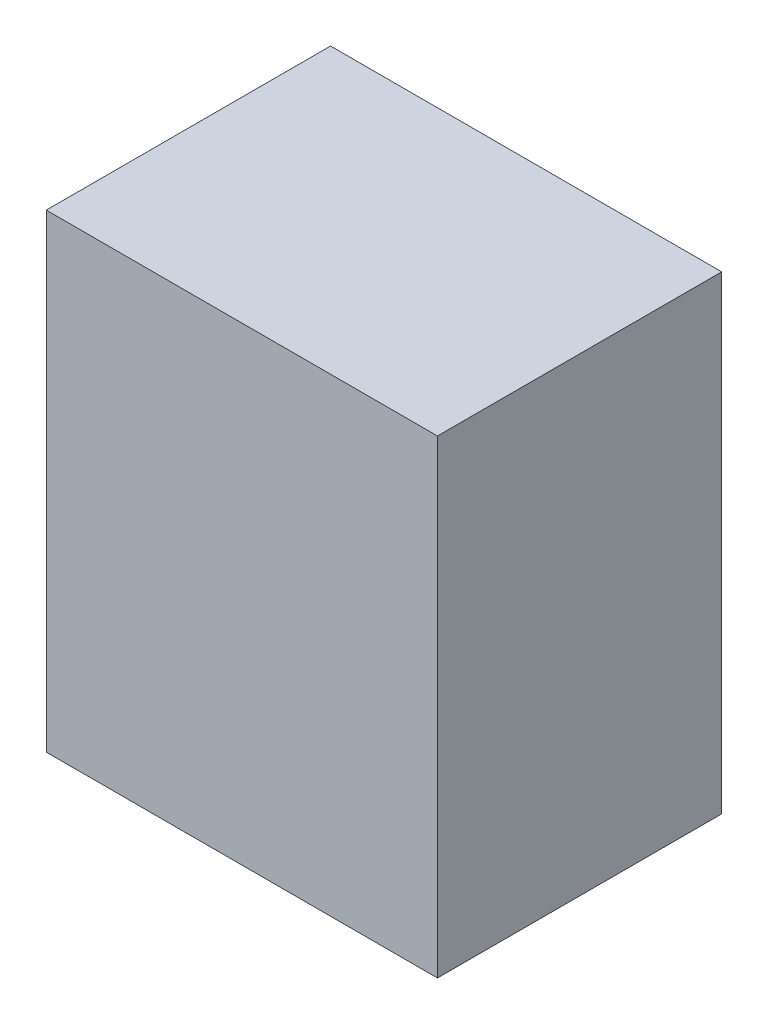
SolidWorks part; units mm, degrees
ref_plane "Front Plane" through (0, 0, 0) normal (0, 0, 1) x (1, 0, 0)
ref_plane "Top Plane" through (0, 0, 0) normal (0, 1, 0) x (1, 0, 0)
ref_plane "Right Plane" through (0, 0, 0) normal (1, 0, 0) x (0, 0, -1)
sketch "Sketch1" plane through (0, 0, 0) normal (0, 0, 1) x (1, 0, 0)
  line L1 (0, 0) -> (38.1, 0)
  line L2 (0, 0) -> (0, 45.72)
  line L3 (0, 45.72) -> (38.1, 45.72)
  line L4 (38.1, 0) -> (38.1, 45.72)
  dimension "D1" = 38.1
  dimension "D2" = 45.72
extrude "Boss-Extrude1" add sketch "Sketch1" along normal blind 27.686
